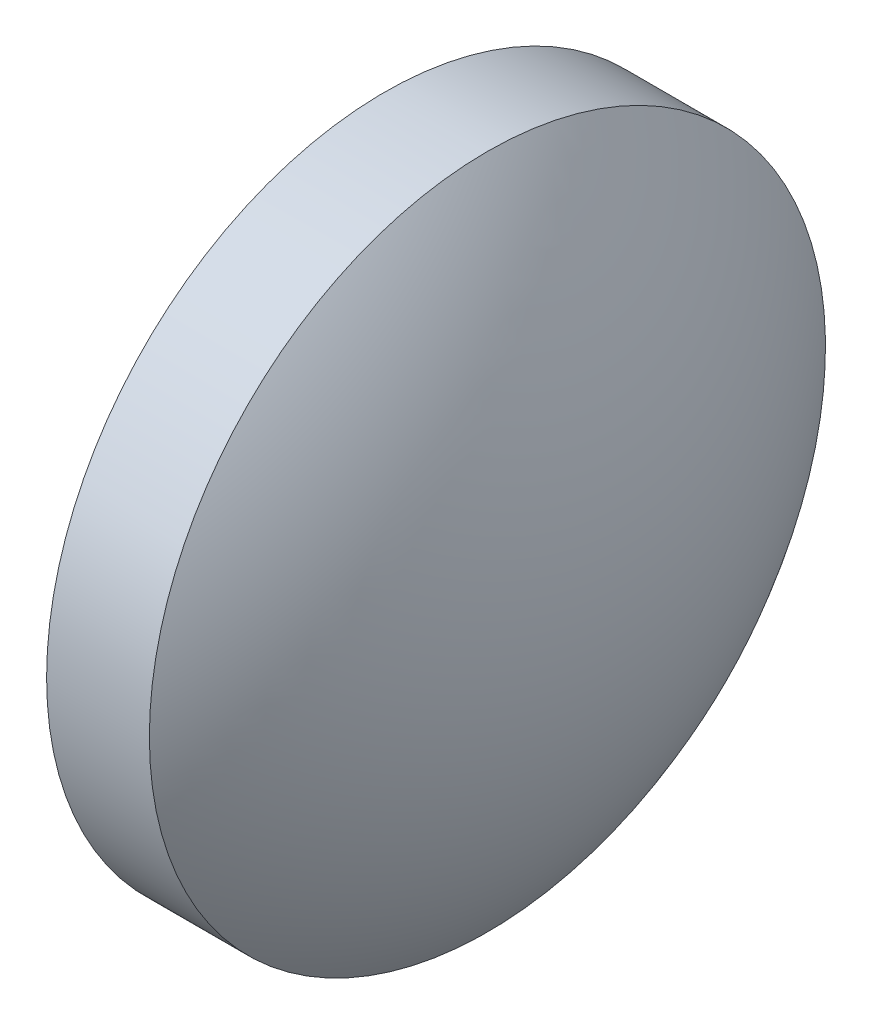
SolidWorks part; units mm, degrees
ref_plane "前视基准面" through (0, 0, 0) normal (0, 0, 1) x (1, 0, 0)
ref_plane "上视基准面" through (0, 0, 0) normal (0, 1, 0) x (1, 0, 0)
ref_plane "右视基准面" through (0, 0, 0) normal (1, 0, 0) x (0, 0, -1)
sketch "草图1" plane through (0, 0, 0) normal (0, 0, 1) x (1, 0, 0)
  line L0 (552.7664, 146.7847) -> (558.9018, 146.7847) construction
  line L1 (553.7079, 146.7847) -> (553.7079, 151.7847)
  line L2 (556.9079, 146.7847) -> (553.7079, 146.7847)
  line L5 (553.7079, 151.7847) -> (555.2279, 151.7847)
  arc A0 (556.9079, 146.7847) -> (555.2279, 151.7847) centre (548.6275, 146.7847) ccw
revolve "旋转1" add sketch "草图1" angle 360 about L0
